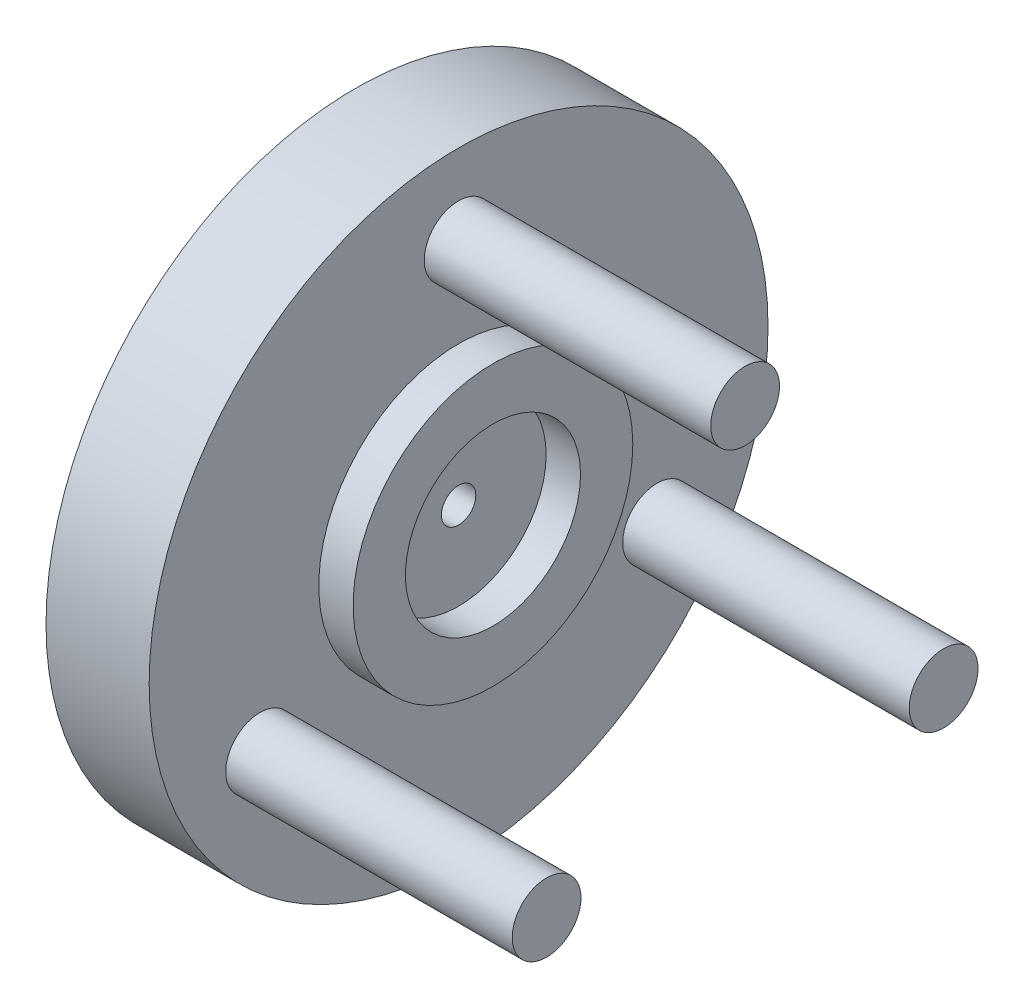
SolidWorks part; units mm, degrees
ref_plane "Front Plane" through (0, 0, 0) normal (0, 0, 1) x (1, 0, 0)
ref_plane "Top Plane" through (0, 0, 0) normal (0, 1, 0) x (1, 0, 0)
ref_plane "Right Plane" through (0, 0, 0) normal (1, 0, 0) x (0, 0, -1)
sketch "Sketch1" plane through (0, 0, 0) normal (1, 0, 0) x (0, 0, -1)
  circle A0 centre (0, 0) radius 1.25
  circle A1 centre (0, 0) radius 2.8
  circle A2 centre (0, 0) radius 27
  dimension "D1" = 2.5
  dimension "D2" = 5.6
  dimension "D3" = 54
extrude "Boss-Extrude2" add sketch "Sketch1" along normal blind 4 contours A2 A1
sketch "Sketch2" plane through (4, 0, 0) normal (1, 0, 0) x (0, 0, -1)
  circle A0 centre (0, 0) radius 2.8
  circle A1 centre (0, 0) radius 1.5
  circle A2 centre (0, 0) radius 36
  circle M1 centre (0, 0) radius 2.8
  circle M2 centre (0, 0) radius 27
  dimension "D1" = 3
  dimension "D2" = 5.6
  dimension "D3" = 72
extrude "Boss-Extrude3" add sketch "Sketch2" along normal blind 5 contours M2 M1 | A1 M1
ref_plane "Plane4" through (9, 0, 0) normal (1, 0, 0) x (0, 0, -1)
sketch "Sketch3" plane through (9, 0, 0) normal (1, 0, 0) x (0, 0, -1)
  circle A4 centre (0, 20) radius 3
  circle A5 centre (17.3205, -10) radius 3
  circle A6 centre (-17.3205, -10) radius 3
  point P14 (0, 0)
  dimension "D1" = 3
  dimension "D2" = 6
extrude "Boss-Extrude4" add sketch "Sketch3" along normal blind 25
ref_plane "Plane5" through (29, 0, 0) normal (1, 0, 0) x (0, 0, -1)
sketch "Sketch4" plane through (9, 0, 0) normal (1, 0, 0) x (0, 0, -1)
  circle A0 centre (0, 0) radius 12.2
  circle A1 centre (0, 0) radius 7.64
  dimension "D1" = 24.4
  dimension "D2" = 15.28
extrude "Boss-Extrude5" add sketch "Sketch4" along normal blind 3
